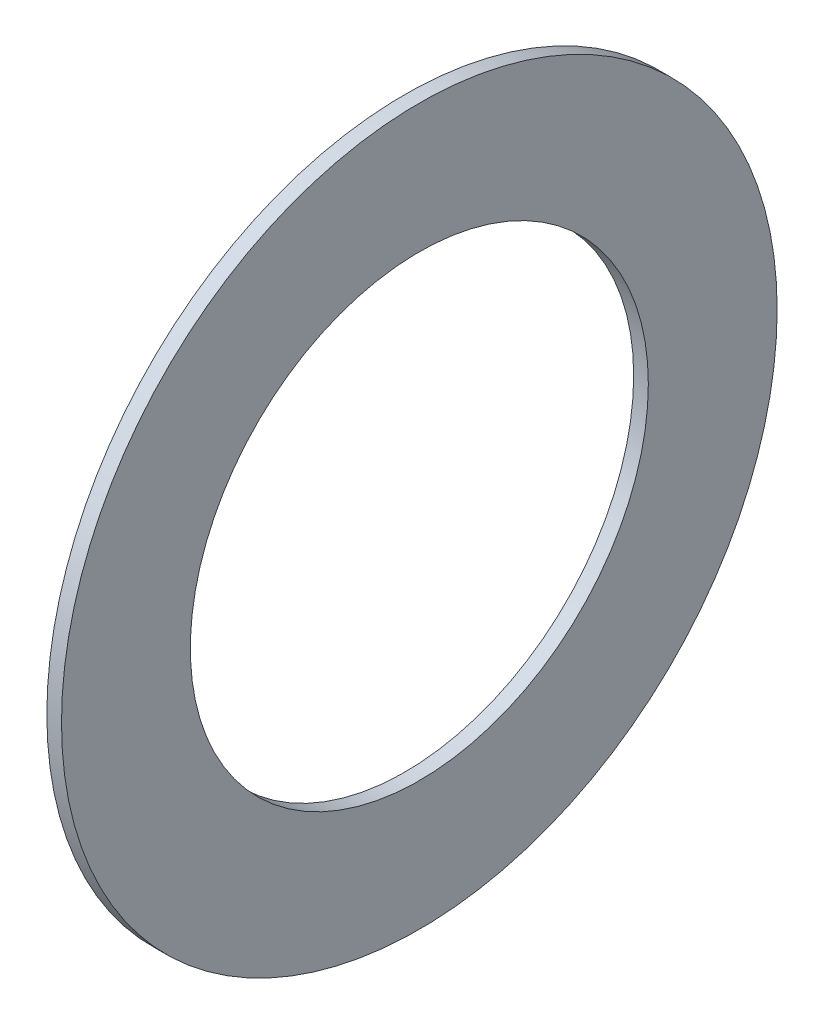
SolidWorks part; units mm, degrees
ref_plane "Front Plane" through (0, 0, 0) normal (0, 0, 1) x (1, 0, 0)
ref_plane "Top Plane" through (0, 0, 0) normal (0, 1, 0) x (1, 0, 0)
ref_plane "Right Plane" through (0, 0, 0) normal (1, 0, 0) x (0, 0, -1)
sketch "Sketch1" plane through (0, 0, 0) normal (1, 0, 0) x (0, 0, -1)
  circle A0 centre (0, 0) radius 19.8438
  circle A1 centre (0, 0) radius 12.7
  dimension "OD" = 39.6875
  dimension "Shaft Dia" = 25.4
extrude "Extrude1" add sketch "Sketch1" along normal blind 0.8128
